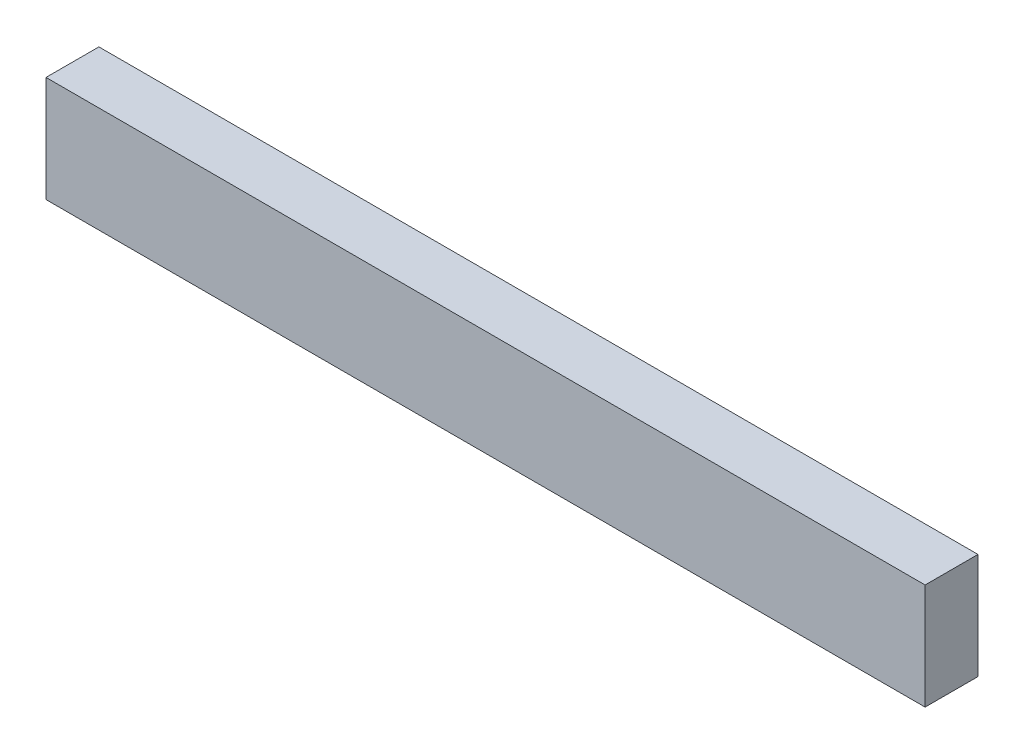
SolidWorks part; units mm, degrees
material "Cedar"
ref_plane "Front Plane" through (0, 0, 0) normal (0, 0, 1) x (1, 0, 0)
ref_plane "Top Plane" through (0, 0, 0) normal (0, 1, 0) x (1, 0, 0)
ref_plane "Right Plane" through (0, 0, 0) normal (1, 0, 0) x (0, 0, -1)
sketch "Sketch1" plane through (0, 0, 0) normal (0, 0, 1) x (1, 0, 0)
  line L1 (-36.079, 29.5758) -> (280.5066, 29.5758)
  line L2 (-36.079, 29.5758) -> (-36.079, -8.5242)
  line L3 (-36.079, -8.5242) -> (280.5066, -8.5242)
  line L4 (280.5066, 29.5758) -> (280.5066, -8.5242)
  dimension "D1" = 316.5856
  dimension "D2" = 38.1
extrude "Boss-Extrude1" add sketch "Sketch1" along normal blind 19.05
